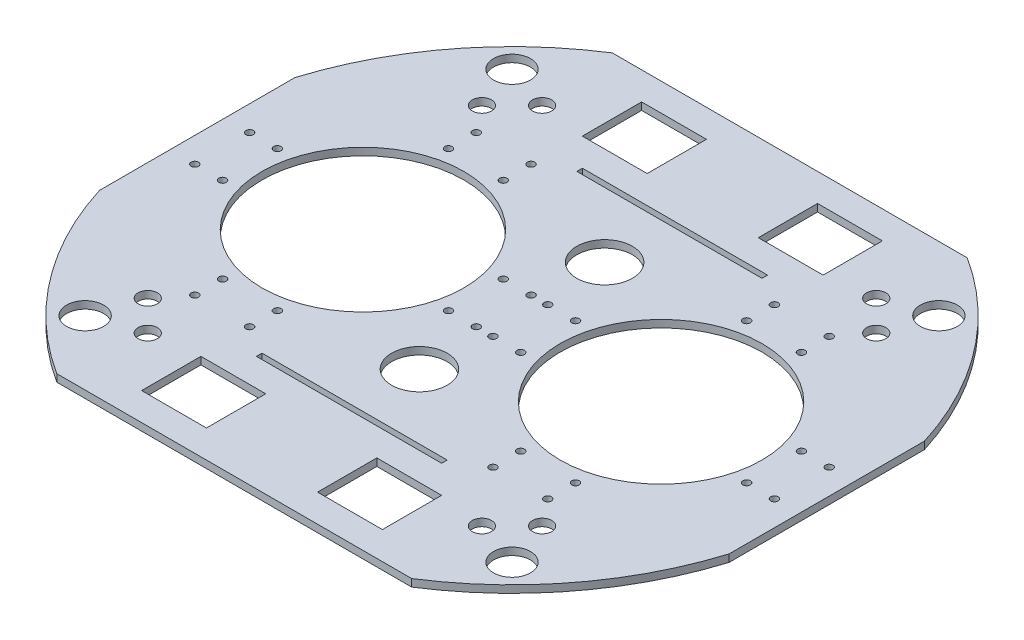
SolidWorks part; units mm, degrees
material "Hexcel AS4C (3000 丝)"
ref_plane "Front" through (0, 0, 0) normal (0, 0, 1) x (1, 0, 0)
ref_plane "Top" through (0, 0, 0) normal (0, 1, 0) x (1, 0, 0)
ref_plane "Right" through (0, 0, 0) normal (1, 0, 0) x (0, 0, -1)
sketch "草图1" plane through (0, 0, 0) normal (0, 1, 0) x (1, 0, 0)
  line L0 (0, 0) -> (20, 0) construction
  line L1 (20, 0) -> (129, 0) construction
  line L2 (0, 0) -> (0, 43.8486) construction
  line L3 (-129, 0) -> (-178, 0) construction
  circle A7 centre (0, 0) radius 178
  point P33 (0, 0)
extrude "凸台-拉伸1" add sketch "草图1" along normal blind 4
sketch "草图2" plane through (0, 4, 0) normal (0, 1, 0) x (1, 0, 0)
  line L0 (0, 0) -> (-125.865, -125.865) construction
  line L1 (125.865, 125.865) -> (115.2584, 115.2584) construction
  line L2 (-125.865, -125.865) -> (-95.8738, -95.8738) construction
  line L3 (-95.8738, -95.8738) -> (-90.2169, -101.5306) construction
  line L5 (-90.2169, -101.5306) -> (-95.1667, -106.4804) construction
  line L6 (-95.1667, -106.4804) -> (-90.2169, -111.4301) construction
  line L7 (-90.2169, -111.4301) -> (-85.2672, -106.4804) construction
  line L8 (-85.2672, -106.4804) -> (-90.2169, -101.5306) construction
  line L9 (-90.2169, -101.5306) -> (-90.2169, -111.4301) construction
  line L20 (-90.2169, -111.4301) -> (-90.2169, -106.4804) construction
  line L21 (-90.2169, -106.4804) -> (-85.2672, -106.4804) construction
  line L29 (0, 0) -> (-125.865, 125.865) construction
  line L38 (0, 0) -> (125.865, 125.865) construction
  line L47 (0, 0) -> (125.865, -125.865) construction
  circle A6 centre (0, 0) radius 178 construction
  circle A7 centre (115.2584, 115.2584) radius 10
  circle A9 centre (-90.2169, -106.4804) radius 5.2
  circle A10 centre (-106.4804, -90.2169) radius 5.2
  circle A11 centre (115.2584, -115.2584) radius 10
  circle A12 centre (-115.2584, -115.2584) radius 10
  circle A13 centre (-115.2584, 115.2584) radius 10
  circle A14 centre (-90.2169, 106.4804) radius 5.2
  circle A15 centre (-106.4804, 90.2169) radius 5.2
  circle A16 centre (106.4804, 90.2169) radius 5.2
  circle A17 centre (90.2169, 106.4804) radius 5.2
  circle A18 centre (90.2169, -106.4804) radius 5.2
  circle A19 centre (106.4804, -90.2169) radius 5.2
  point P27 (0, 0)
  point P43 (0, 0)
  dimension "D1" = 4
  dimension "D2" = 4
extrude "切除-拉伸1" cut sketch "草图2" against normal blind 10
sketch "草图4" plane through (0, 0, 0) normal (0, -1, 0) x (1, 0, 0)
  circle A1 centre (80.5, 0) radius 54.5
  circle A3 centre (-80.5, 0) radius 54.5
  point P3 (0, 0)
  point P4 (0, 0)
extrude "切除-拉伸2" cut sketch "草图4" against normal blind 10
sketch "草图5" plane through (0, 4, 0) normal (0, 1, 0) x (1, 0, 0)
  line L0 (0, 0) -> (-24, 0) construction
  line L1 (-24, 0) -> (-24, 20) construction
  line L2 (-24, 0) -> (-24, -20) construction
  line L3 (-12, 0) -> (-12, -14.8) construction
  line L4 (-12, -14.8) -> (-19.5, -14.8) construction
  line L5 (-12, -14.8) -> (-4.5, -14.8) construction
  line L6 (0, 0) -> (0, 20) construction
  line L7 (-24, 0) -> (-26, 0) construction
  circle A82 centre (-19.5, -14.8) radius 2
  circle A83 centre (-4.5, -14.8) radius 2
  circle A84 centre (-4.5, 14.8) radius 2
  circle A85 centre (-19.5, 14.8) radius 2
  circle A86 centre (-80.5, 0) radius 54.5 construction
  circle A87 centre (4.5, -14.8) radius 2
  circle A88 centre (19.5, -14.8) radius 2
  circle A89 centre (19.5, 14.8) radius 2
  circle A90 centre (4.5, 14.8) radius 2
  circle A91 centre (-65.7, -61) radius 2
  circle A92 centre (-65.7, -76) radius 2
  circle A93 centre (-95.3, -61) radius 2
  circle A94 centre (-95.3, -76) radius 2
  circle A95 centre (-141.5, -14.8) radius 2
  circle A96 centre (-156.5, -14.8) radius 2
  circle A97 centre (-141.5, 14.8) radius 2
  circle A98 centre (-156.5, 14.8) radius 2
  circle A99 centre (-95.3, 61) radius 2
  circle A100 centre (-95.3, 76) radius 2
  circle A101 centre (-65.7, 61) radius 2
  circle A102 centre (-65.7, 76) radius 2
  circle A103 centre (95.3, 76) radius 2
  circle A104 centre (95.3, 61) radius 2
  circle A105 centre (65.7, 76) radius 2
  circle A106 centre (65.7, 61) radius 2
  circle A107 centre (156.5, -14.8) radius 2
  circle A108 centre (141.5, -14.8) radius 2
  circle A109 centre (156.5, 14.8) radius 2
  circle A110 centre (141.5, 14.8) radius 2
  circle A111 centre (65.7, -76) radius 2
  circle A112 centre (65.7, -61) radius 2
  circle A113 centre (95.3, -76) radius 2
  circle A114 centre (95.3, -61) radius 2
  point P53 (-80.5, 0)
  point P78 (80.5, 0)
extrude "切除-拉伸3" cut sketch "草图5" against normal blind 10
sketch "草图8" plane through (0, 0, 0) normal (0, -1, 0) x (1, 0, 0)
  line L0 (0, 0) -> (170, 0) construction
  line L1 (170, 0) -> (170, 52.7636) construction
  line L2 (0, 0) -> (0, 150) construction
  line L3 (0, 150) -> (95.8332, 150) construction
  line L4 (95.8332, 150) -> (0, 150)
  line L5 (0, 150) -> (-95.8332, 150)
  line L6 (170, 52.7636) -> (170, 0)
  line L7 (170, 0) -> (170, -52.7636)
  line L8 (0, -150) -> (-95.8332, -150)
  line L9 (95.8332, -150) -> (0, -150)
  line L10 (-170, 0) -> (-170, -52.7636)
  line L11 (-170, 52.7636) -> (-170, 0)
  circle A0 centre (0, 0) radius 178 construction
  arc A1 (-170, 52.7636) -> (-170, -52.7636) centre (0, 0) ccw
  arc A2 (95.8332, 150) -> (-95.8332, 150) centre (0, 0) ccw
  arc A3 (170, -52.7636) -> (170, 52.7636) centre (0, 0) ccw
  arc A4 (-95.8332, -150) -> (95.8332, -150) centre (0, 0) ccw
extrude "切除-拉伸4" cut sketch "草图8" against normal blind 10
sketch "草图11" plane through (0, 0, 0) normal (0, -1, 0) x (1, 0, 0)
  line L0 (0, -150) -> (0, -85) construction
  line L1 (95.8332, -150) -> (-95.8332, -150) construction
  line L2 (0, -85) -> (50, -85) construction
  line L3 (50, -85) -> (50, -88) construction
  line L4 (-50, -85) -> (50, -85)
  line L5 (50, -85) -> (50, -88)
  line L6 (50, -88) -> (-50, -88)
  line L7 (-50, -85) -> (-50, -88)
  line L8 (0, 0) -> (80.5, 0) construction
  line L9 (0, -150) -> (80, -150) construction
  line L10 (80, -150) -> (80, -135) construction
  line L11 (65, -135) -> (30, -135)
  line L12 (50, -88) -> (50, -103) construction
  line L13 (50, -103) -> (80, -103) construction
  line L15 (65, -103) -> (30, -103)
  line L17 (-80, -119) -> (-65, -119) construction
  line L18 (-65, -119) -> (-65, -103)
  line L19 (-65, -119) -> (-65, -135)
  line L20 (80, -119) -> (65, -119) construction
  line L21 (-50, 85) -> (-50, 88)
  line L22 (65, -103) -> (65, -135)
  line L23 (50, 85) -> (50, 88)
  line L24 (50, 88) -> (-50, 88)
  line L25 (-50, 85) -> (50, 85)
  line L31 (0, -135) -> (0, -103) construction
  line L32 (0, -103) -> (0, -119) construction
  line L33 (0, -119) -> (30, -119) construction
  line L34 (30, -119) -> (30, -103)
  line L35 (30, -119) -> (30, -135)
  line L36 (-30, -119) -> (-30, -135)
  line L37 (-30, -119) -> (-30, -103)
  line L38 (-30, -103) -> (-65, -103)
  line L39 (-30, -135) -> (-65, -135)
  line L40 (-65, 119) -> (-65, 103)
  line L41 (-30, 103) -> (-65, 103)
  line L42 (-30, 119) -> (-30, 103)
  line L43 (-30, 119) -> (-30, 135)
  line L44 (-30, 135) -> (-65, 135)
  line L45 (-65, 119) -> (-65, 135)
  line L46 (65, 103) -> (65, 135)
  line L47 (65, 103) -> (30, 103)
  line L48 (30, 119) -> (30, 103)
  line L49 (30, 119) -> (30, 135)
  line L50 (65, 135) -> (30, 135)
  point P10 (0, -88)
extrude "切除-拉伸5" cut sketch "草图11" against normal blind 10
sketch "草图13" plane through (0, 0, 0) normal (0, -1, 0) x (1, 0, 0)
  line L0 (0, 0) -> (0, -50) construction
  line L1 (0, 0) -> (26, 0) construction
  circle A0 centre (0, -50) radius 15
  circle A1 centre (80.5, 0) radius 54.5 construction
  circle A2 centre (0, 50) radius 15
extrude "切除-拉伸6" cut sketch "草图13" against normal blind 10
